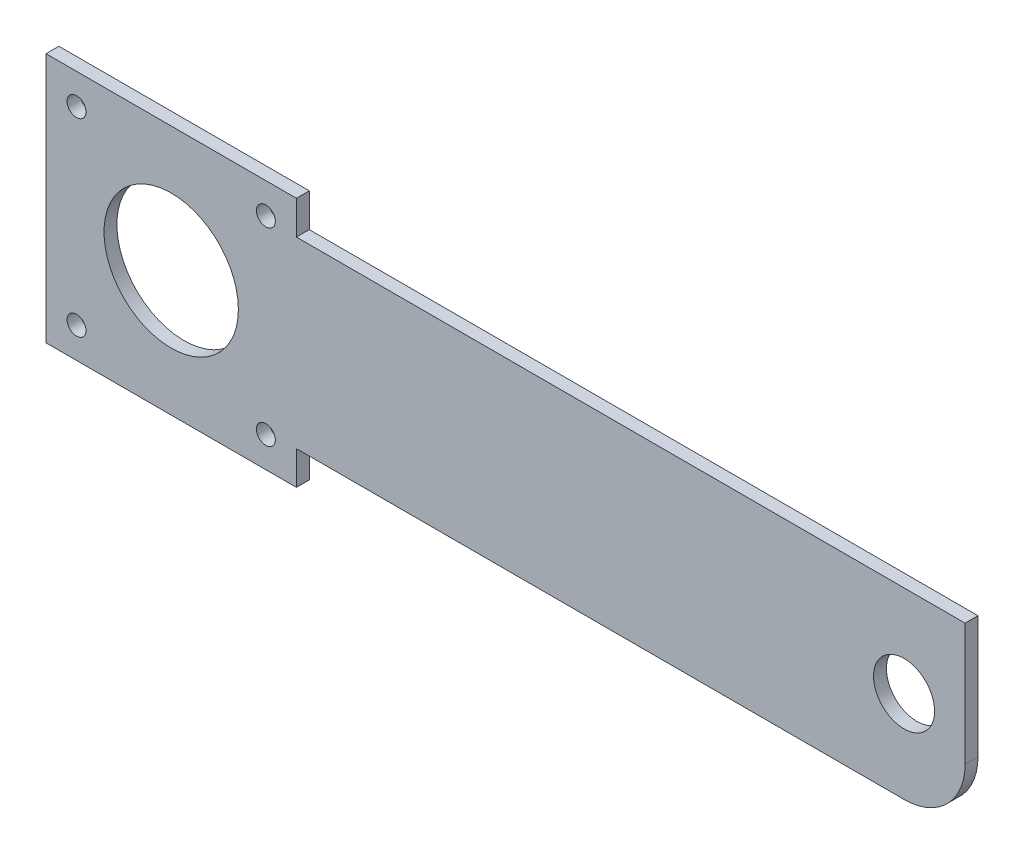
SolidWorks part; units mm, degrees
material "Aluminio 3105"
ref_plane "Alzado" through (0, 0, 0) normal (0, 0, 1) x (1, 0, 0)
ref_plane "Planta" through (0, 0, 0) normal (0, 1, 0) x (1, 0, 0)
ref_plane "Vista lateral" through (0, 0, 0) normal (1, 0, 0) x (0, 0, -1)
sketch "Croquis1" plane through (0, 0, 0) normal (0, 0, 1) x (1, 0, 0)
  line L5 (158.2088, -21.4058) -> (158.2088, 8.5942)
  line L6 (-7.2912, -6.4058) -> (158.2088, -6.4058) construction
  line L7 (7.7088, 14.0942) -> (48.7088, 14.0942)
  line L8 (12.7088, -21.9058) -> (43.7088, -21.9058) construction
  line L9 (12.7088, -21.9058) -> (12.7088, 9.0942) construction
  line L10 (12.7088, 9.0942) -> (43.7088, 9.0942) construction
  line L11 (43.7088, -21.9058) -> (43.7088, 9.0942) construction
  line L12 (12.7088, -21.9058) -> (43.7088, 9.0942) construction
  line L13 (12.7088, 9.0942) -> (43.7088, -21.9058) construction
  line L14 (48.7088, -26.9058) -> (48.7088, -21.4058)
  line L15 (7.7088, -26.9058) -> (48.7088, -26.9058)
  line L18 (48.7088, 8.5942) -> (48.7088, 14.0942)
  line L19 (7.7088, -26.9058) -> (7.7088, 14.0942) construction
  line L20 (48.7088, 8.5942) -> (158.2088, 8.5942)
  line L21 (48.7088, -26.9058) -> (48.7088, 14.0942) construction
  line L22 (48.7088, -21.4058) -> (158.2088, -21.4058)
  line L23 (7.7088, -26.9058) -> (7.7088, 14.0942)
  circle A4 centre (12.7088, -21.9058) radius 1.55
  circle A5 centre (12.7088, 9.0942) radius 1.55
  circle A6 centre (43.7088, 9.0942) radius 1.55
  circle A7 centre (43.7088, -21.9058) radius 1.55
  point P2 (28.2088, -6.4058)
  point P29 (28.2088, -6.4058)
  dimension "D3" = 31
  dimension "D6" = 3.1
  dimension "D1" = 130
  dimension "D5" = 5
  dimension "D7" = 4
extrude "Saliente-Extruir1" add sketch "Croquis1" along normal blind 2.11
sketch "Croquis5" plane through (0, 0, 2.11) normal (0, 0, 1) x (1, 0, 0)
  circle A0 centre (28.2088, -6.4058) radius 11
  dimension "D1" = 22
extrude "Cortar-Extruir1" cut sketch "Croquis5" against normal up to surface (2.11 mm away) up to face at (65.8338, -6.4058, 0)
sketch "Croquis6" plane through (0, 0, 2.11) normal (0, 0, 1) x (1, 0, 0)
  line L0 (158.2088, -21.4058) -> (158.2088, 8.5942) construction
  circle A0 centre (148.2088, -6.4058) radius 5
  dimension "D2" = 10
  dimension "D1" = 10
extrude "Cortar-Extruir2" cut sketch "Croquis6" against normal up to surface (2.11 mm away) up to face at (39.2088, -6.4058, 0)
fillet "Redondeo1" radius 10 1 edges at (158.2088, -21.4058, 1.055)
